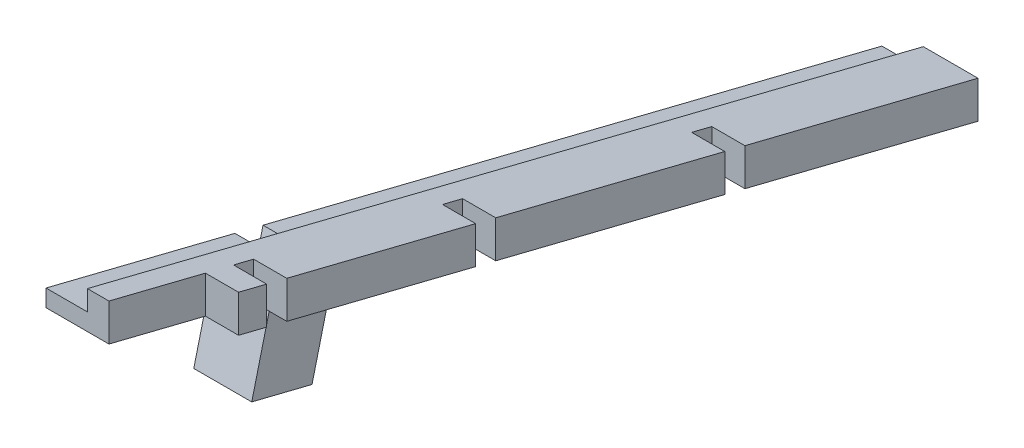
SolidWorks part; units mm, degrees
ref_plane "Front Plane" through (0, 0, 0) normal (0, 0, 1) x (1, 0, 0)
ref_plane "Top Plane" through (0, 0, 0) normal (0, 1, 0) x (1, 0, 0)
ref_plane "Right Plane" through (0, 0, 0) normal (1, 0, 0) x (0, 0, -1)
sketch "Sketch1" plane through (0, 0, 0) normal (1, 0, 0) x (0, 0, -1)
  line L0 (0, 0) -> (117.1645, 0) construction
  line L1 (0, 0) -> (89.2672, -22.2568)
  line L2 (0, 0) -> (0, -4.5)
  line L3 (0, -4.5) -> (89.2672, -26.7568)
  line L4 (89.2672, -26.7568) -> (89.2672, -22.2568)
  line L5 (61.1286, -19.7411) -> (61.1286, -15.2411)
  line L6 (58.7029, -19.1363) -> (58.7029, -14.6363)
  line L7 (31.0495, -12.2415) -> (31.0495, -7.7415)
  line L8 (28.6237, -11.6367) -> (28.6237, -7.1367)
  line L9 (5.8218, -5.9515) -> (5.8218, -1.4515)
  line L10 (3.396, -5.3467) -> (3.396, -0.8467)
  dimension "D1" = 14
  dimension "D2" = 29
  dimension "D3" = 31.5
  dimension "D4" = 60
  dimension "D5" = 62.5
  dimension "D6" = 86
  dimension "D7" = 88.5
  dimension "D8" = 92
  dimension "D9" = 4.5
extrude "Side comb" add sketch "Sketch1" along normal blind 4 contours L3 L10 L1 L2 | L9 L3 L8 L1 | L7 L3 L6 L1 | L5 L3 L4 L1
sketch "Sketch2" plane through (0, 0, 0) normal (-1, 0, 0) x (0, 0, 1)
  line L1 (-89.2672, -22.2568) -> (-89.2672, -26.7568)
  line L4 (-89.2672, -22.2568) -> (11.6435, 2.9031)
  line L5 (0, 0) -> (0, -4.5) construction
  line L6 (-89.2672, -26.7568) -> (11.6435, -1.5969)
  line L7 (11.6435, 2.9031) -> (11.6435, -1.5969)
  dimension "D1" = 12
extrude "Side spacer" add sketch "Sketch2" along normal blind 2.6
sketch "Sketch3" plane through (-2.6, 0, 0) normal (-1, 0, 0) x (0, 0, 1)
  line L0 (-89.2672, -24.6956) -> (11.6435, 0.4643)
  line L1 (-89.2672, -22.2568) -> (-89.2672, -26.7568) construction
  line L2 (11.6435, -1.5969) -> (11.6435, 2.9031) construction
  line L3 (-89.2672, -26.7568) -> (11.6435, -1.5969) construction
  line L4 (-89.2672, -24.6956) -> (-89.2672, -26.7568)
  line L5 (-89.2672, -26.7568) -> (11.6435, -1.5969)
  line L6 (11.6435, -1.5969) -> (11.6435, 0.4643)
  dimension "D1" = 2
extrude "Narrow support" add sketch "Sketch3" along normal blind 5
sketch "Sketch4" plane through (-7.6, 0, 0) normal (-1, 0, 0) x (0, 0, 1)
  line L0 (-89.2672, -24.6956) -> (-80.5345, -22.5183)
  line L1 (11.6435, 0.4643) -> (-89.2672, -24.6956) construction
  line L2 (-80.5345, -22.5183) -> (-80.5345, -24.5795)
  line L3 (-89.2672, -26.7568) -> (11.6435, -1.5969) construction
  line L4 (-80.5345, -24.5795) -> (-89.2672, -26.7568)
  line L5 (-89.2672, -26.7568) -> (-89.2672, -24.6956)
  line L6 (11.6435, 0.4643) -> (11.6435, -1.5969)
  line L7 (11.6435, -1.5969) -> (2.9109, -3.7742)
  line L8 (2.9109, -3.7742) -> (2.9109, -1.713)
  line L9 (11.6435, 0.4643) -> (-89.2672, -24.6956) construction
  line L10 (2.9109, -1.713) -> (11.6435, 0.4643)
  dimension "D1" = 9
  dimension "D2" = 9
sketch "Sketch5" plane through (0, -2.296, 0.5725) normal (0, 0.9703, -0.2419) x (1, 0, 0)
  line L0 (-2.6, -11.41) -> (-2.6, 92.59) construction
  line L1 (-7.6, 92.59) -> (-2.6, 92.59) construction
  line L2 (-2.6, 12.09) -> (-7.6, 12.09) construction
  line L3 (-7.6, -11.41) -> (-7.6, 92.59) construction
  line L4 (-9.85, 88.09) -> (-2.6, 88.09) construction
  line L5 (-9.85, -7.91) -> (-2.6, -7.91) construction
  circle A0 centre (-9.85, 88.09) radius 1.75
  circle A1 centre (-9.85, -7.91) radius 1.75
  dimension "D4" = 3.5
  dimension "D1" = 7.25
  dimension "D2" = 100.5
  dimension "D5" = 76
  dimension "D6" = 4.5
sketch "Sketch6" plane through (0, -4.2366, 1.0563) normal (0, -0.9703, 0.2419) x (1, 0, 0)
  line L2 (-2.6, -12.09) -> (-7.6, -12.09) construction
  line L3 (-2.6, -12.09) -> (-7.6, -12.09)
  line L4 (-2.6, -15.59) -> (-7.6, -15.59)
  line L5 (-7.6, -93.0886) -> (-7.6, 10.9114) construction
  line L6 (-7.6, -15.59) -> (-7.6, -17.59)
  line L7 (-7.6, -17.59) -> (-0.6, -17.59)
  line L8 (-0.6, -10.09) -> (-0.6, -17.59)
  line L9 (-0.6, -10.09) -> (-7.6, -10.09)
  line L10 (-7.6, -10.09) -> (-7.6, -12.09)
  line L11 (-2.6, -15.59) -> (-2.6, -12.09)
  dimension "D1" = 2
  dimension "D2" = 2
  dimension "D4" = 3.5
sketch "Sketch7" plane through (0, -4.2366, 1.0563) normal (0, -0.9703, 0.2419) x (1, 0, 0)
  line L0 (-7.6, -12.09) -> (-7.6, -15.59)
  line L1 (-7.6, -15.59) -> (-2.6, -15.59)
  line L2 (-2.6, -15.59) -> (-2.6, -12.09)
  line L3 (-2.6, -12.09) -> (-7.6, -12.09)
extrude "Gap for support bar" cut sketch "Sketch7" against normal up to vertex (2 mm away)
extrude "Support bar sides" add sketch "Sketch6" along normal blind 8.5
sketch "Sketch8" plane through (0, -12.4841, 3.1126) normal (0, -0.9703, 0.2419) x (1, 0, 0)
  line L0 (-0.6, -17.59) -> (-0.6, -10.09) construction
  line L1 (-7.6, -10.09) -> (-0.6, -10.09)
  line L2 (-7.6, -10.09) -> (-7.6, -17.59)
  line L3 (-7.6, -17.59) -> (-0.6, -17.59)
  line L4 (-0.6, -10.09) -> (-0.6, -17.59)
extrude "Support bar bottom" add sketch "Sketch8" along normal blind 2
